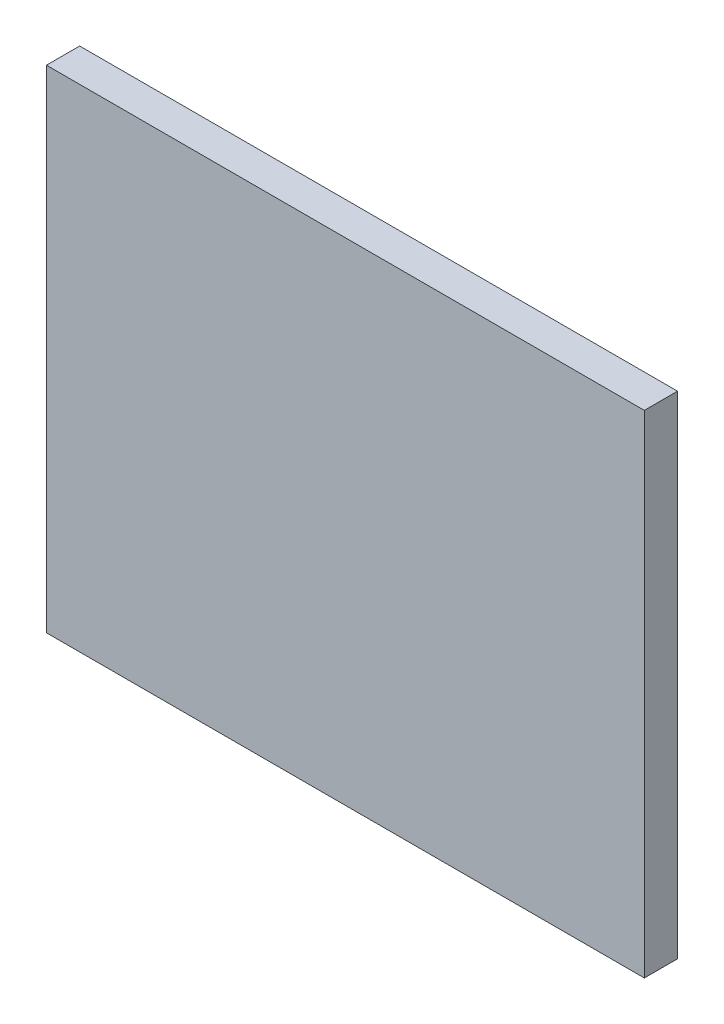
SolidWorks part; units mm, degrees
ref_plane "Alzado" through (0, 0, 0) normal (0, 0, 1) x (1, 0, 0)
ref_plane "Planta" through (0, 0, 0) normal (0, 1, 0) x (1, 0, 0)
ref_plane "Vista lateral" through (0, 0, 0) normal (1, 0, 0) x (0, 0, -1)
sketch "Croquis1" plane through (0, 0, 0) normal (0, 0, 1) x (1, 0, 0)
  line L1 (-45, -37) -> (45, -37)
  line L2 (-45, -37) -> (-45, 37)
  line L3 (-45, 37) -> (45, 37)
  line L4 (45, -37) -> (45, 37)
  line L5 (-45, -37) -> (45, 37) construction
  line L6 (-45, 37) -> (45, -37) construction
  point P0 (0, 0)
  dimension "D1" = 90
  dimension "D2" = 74
extrude "Saliente-Extruir1" add sketch "Croquis1" along normal blind 5
sketch "Croquis3" plane through (0, 0, 0) normal (0, 0, -1) x (-1, 0, 0)
  line L0 (-45, 0) -> (45, 0) construction
  line L1 (-40, 32.5) -> (-10, 32.5)
  line L2 (-40, 32.5) -> (-40, 7.5)
  line L3 (-40, 7.5) -> (-10, 7.5)
  line L4 (-10, 32.5) -> (-10, 7.5)
  line L5 (-40, 32.5) -> (-10, 7.5) construction
  line L6 (-40, 7.5) -> (-10, 32.5) construction
  line L7 (-45, -37) -> (-45, 37) construction
  line L8 (45, 37) -> (45, -37) construction
  line L9 (0, 37) -> (0, -37) construction
  line L10 (-45, 37) -> (45, 37) construction
  line L11 (45, -37) -> (-45, -37) construction
  line L12 (-40, -7.5) -> (-10, -7.5)
  line L13 (-10, -32.5) -> (-10, -7.5)
  line L14 (-40, -32.5) -> (-10, -32.5)
  line L15 (-40, -32.5) -> (-40, -7.5)
  line L16 (40, 7.5) -> (10, 7.5)
  line L17 (10, 32.5) -> (10, 7.5)
  line L18 (40, 32.5) -> (10, 32.5)
  line L19 (40, 32.5) -> (40, 7.5)
  line L20 (40, -32.5) -> (40, -7.5)
  line L21 (40, -32.5) -> (10, -32.5)
  line L22 (10, -32.5) -> (10, -7.5)
  line L23 (40, -7.5) -> (10, -7.5)
  point P0 (-25, 20)
  dimension "D1" = 30
  dimension "D2" = 25
  dimension "D3" = 25
  dimension "D4" = 20
extrude "Saliente-Extruir2" add sketch "Croquis3" along normal blind 1
